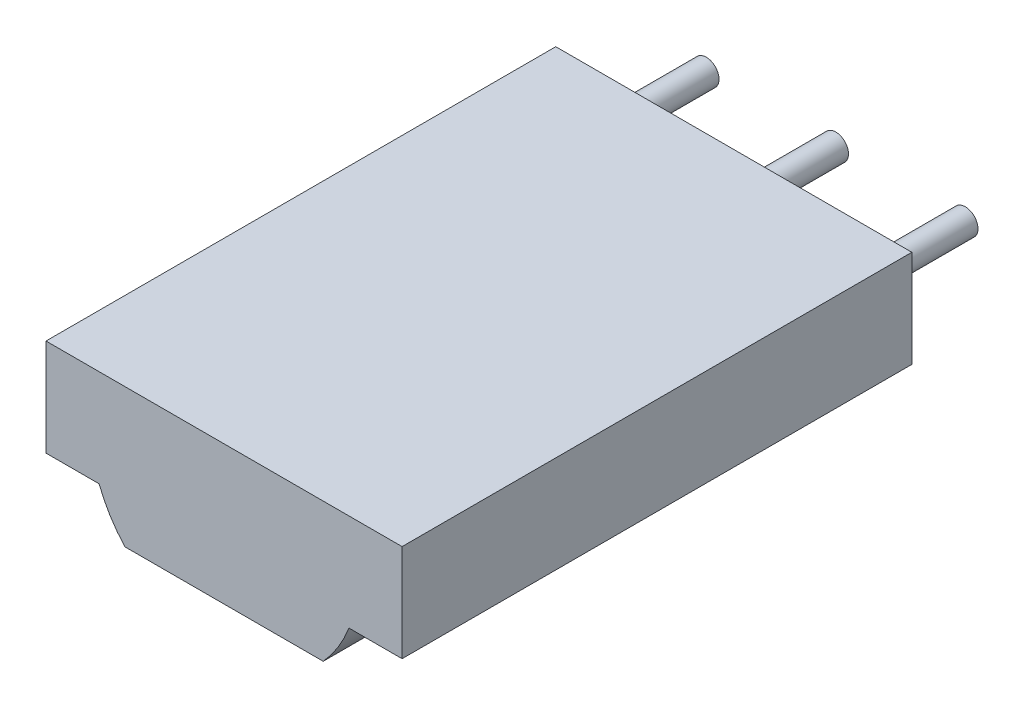
SolidWorks part; units mm, degrees
ref_plane "Front Plane" through (0, 0, 0) normal (0, 0, 1) x (1, 0, 0)
ref_plane "Top Plane" through (0, 0, 0) normal (0, 1, 0) x (1, 0, 0)
ref_plane "Right Plane" through (0, 0, 0) normal (1, 0, 0) x (0, 0, -1)
sketch "Sketch1" plane through (0, 0, 0) normal (0, 0, 1) x (1, 0, 0)
  line L0 (0.0885, 0.9525) -> (-0.9525, 0.9525)
  line L1 (-0.9525, 0.9525) -> (-0.9525, -0.9525)
  line L2 (-0.9525, -0.9525) -> (0.0885, -0.9525)
  line L3 (0.5947, -1.77) -> (4.4852, -1.77)
  line L4 (4.9914, -0.9525) -> (6.0325, -0.9525)
  line L5 (6.0325, -0.9525) -> (6.0325, 0.9525)
  line L6 (6.0325, 0.9525) -> (4.9914, 0.9525)
  line L7 (4.9914, 0.9525) -> (0.0885, 0.9525)
  arc A0 (0.0885, -0.9525) -> (0.5947, -1.77) centre (2.54, 0) ccw
  arc A1 (4.4852, -1.77) -> (4.9914, -0.9525) centre (2.5399, 0) ccw
extrude "Component_Outline" add sketch "Sketch1" along normal blind 10 separate body
sketch "Sketch2" plane through (0, 0, 0) normal (0, 0, 1) x (1, 0, 0)
  circle A0 centre (0, 0) radius 0.25
extrude "1" add sketch "Sketch2" against normal blind 2 separate body
sketch "Sketch3" plane through (0, 0, 0) normal (0, 0, 1) x (1, 0, 0)
  circle A0 centre (2.54, 0) radius 0.25
extrude "2" add sketch "Sketch3" against normal blind 2 separate body
sketch "Sketch4" plane through (0, 0, 0) normal (0, 0, 1) x (1, 0, 0)
  circle A0 centre (5.08, 0) radius 0.25
extrude "3" add sketch "Sketch4" against normal blind 2 separate body
sketch3d "3DSketch1"
  line L0 (0, 0, 0) -> (1, 0, 0)
  line L1 (0, 0, 0) -> (0, 1, 0)
  line L2 (0, 0, 0) -> (0, 0, 1)
  point P0 (0, 0, 0)
